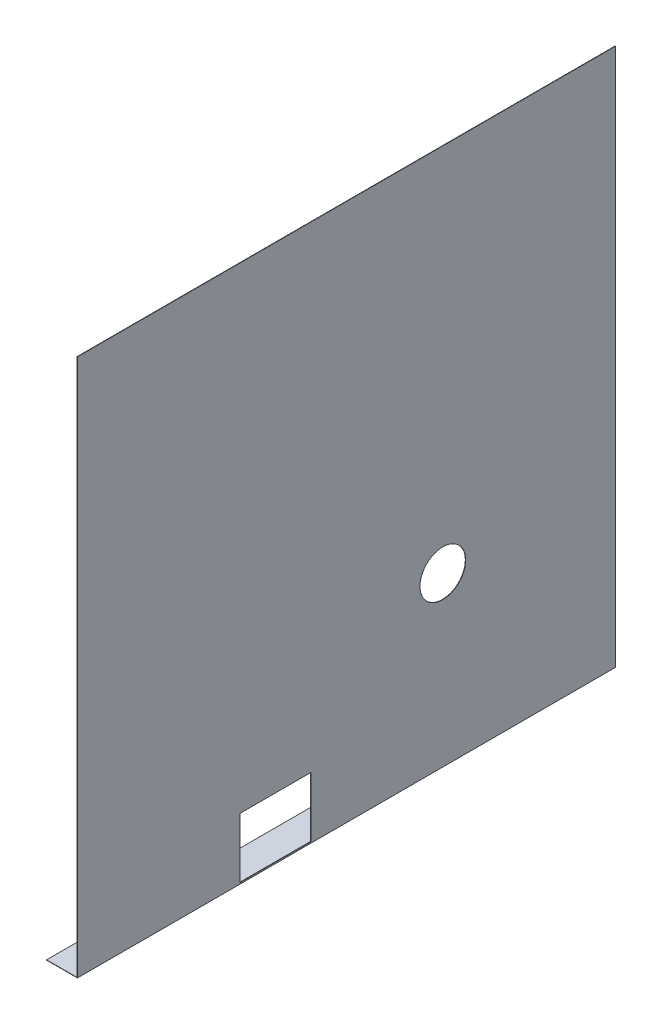
SolidWorks part; units mm, degrees
ref_plane "Front Plane" through (0, 0, 0) normal (0, 0, 1) x (1, 0, 0)
ref_plane "Top Plane" through (0, 0, 0) normal (0, 1, 0) x (1, 0, 0)
ref_plane "Right Plane" through (0, 0, 0) normal (1, 0, 0) x (0, 0, -1)
sketch "Sketch1" plane through (0, 0, 0) normal (0, 0, 1) x (1, 0, 0)
  line L0 (0, 0) -> (0, 530)
  line L1 (0, 530) -> (-0.35, 530)
  line L2 (-0.35, 530) -> (-0.35, 0.35)
  line L3 (-0.35, 0.35) -> (-30.35, 0.35)
  line L4 (-30.35, 0.35) -> (-30.35, 0)
  line L5 (-30.35, 0) -> (0, 0)
  dimension "D1" = 530
  dimension "D2" = 30
  dimension "D3" = 0.35
  dimension "D4" = 0.35
extrude "Boss-Extrude1" add sketch "Sketch1" along normal blind 530
sketch "Sketch2" plane through (-0.35, 0, 0) normal (-1, 0, 0) x (0, 0, 1)
  line L0 (530, 530) -> (530, 0.35) construction
  line L1 (530, 0.35) -> (0, 0.35) construction
  circle A0 centre (170, 165.35) radius 22.5
  dimension "D1" = 360
  dimension "D2" = 165
  dimension "D3" = 45
extrude "Cut-Extrude1" cut sketch "Sketch2" against normal blind 530
sketch "Sketch3" plane through (-0.35, 0, 0) normal (-1, 0, 0) x (0, 0, 1)
  line L0 (300, 1.35) -> (300, 60.35)
  line L2 (300, 60.35) -> (370, 60.35)
  line L3 (370, 60.35) -> (370, 1.35)
  line L5 (370, 1.35) -> (300, 1.35)
  line L6 (530, 530) -> (530, 0.35) construction
  line L7 (530, 0.35) -> (0, 0.35) construction
  point P2 (0, 0)
  point P10 (300, 0.35)
  dimension "D1" = 70
  dimension "D2" = 59
  dimension "D3" = 160
  dimension "D4" = 1
extrude "Cut-Extrude2" cut sketch "Sketch3" against normal blind 530
